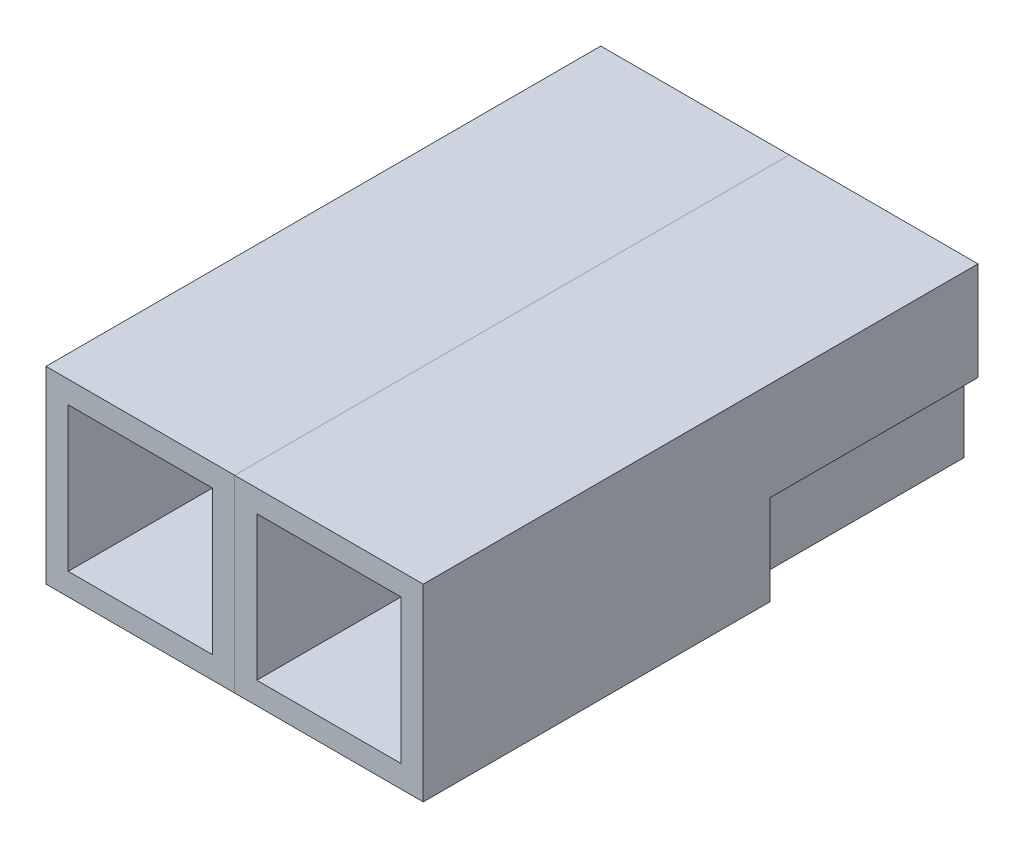
SolidWorks part; units mm, degrees
ref_plane "Front Plane" through (0, 0, 0) normal (0, 0, 1) x (1, 0, 0)
ref_plane "Top Plane" through (0, 0, 0) normal (0, 1, 0) x (1, 0, 0)
ref_plane "Right Plane" through (0, 0, 0) normal (1, 0, 0) x (0, 0, -1)
sketch "Sketch1" plane through (0, 0, 0) normal (0, 0, 1) x (1, 0, 0)
  line L1 (-11.0964, -1.4955) -> (-2.4604, -1.4955)
  line L2 (-11.0964, -1.4955) -> (-11.0964, -10.1315)
  line L3 (-11.0964, -10.1315) -> (-2.4604, -10.1315)
  line L4 (-2.4604, -1.4955) -> (-2.4604, -10.1315)
  dimension "D1" = 8.636
  dimension "D2" = 8.636
extrude "Extrude1" add sketch "Sketch1" along normal blind 25.4
sketch "Sketch2" plane through (0, 0, 25.4) normal (0, 0, 1) x (1, 0, 0)
  line L0 (-11.0964, -1.4955) -> (-11.0964, -10.1315) construction
  line L1 (-10.0804, -2.5115) -> (-3.4764, -2.5115)
  line L2 (-10.0804, -2.5115) -> (-10.0804, -9.1155)
  line L3 (-10.0804, -9.1155) -> (-3.4764, -9.1155)
  line L4 (-3.4764, -2.5115) -> (-3.4764, -9.1155)
  line L5 (-2.4604, -10.1315) -> (-2.4604, -1.4955) construction
  line L6 (-2.4604, -1.4955) -> (-11.0964, -1.4955) construction
  line L7 (-11.0964, -10.1315) -> (-2.4604, -10.1315) construction
  dimension "D1" = 1.016
  dimension "D2" = 1.016
  dimension "D3" = 1.016
  dimension "D4" = 1.016
extrude "Extrude2" cut sketch "Sketch2" against normal blind 12.7
sketch "Sketch3" plane through (0, 0, 0) normal (0, 0, -1) x (-1, 0, 0)
  line L4 (2.9684, -2.0035) -> (2.9684, -6.0053)
  line L5 (10.5884, -2.0035) -> (10.5884, -6.0053)
  line L7 (2.9684, -6.0053) -> (10.5884, -6.0053)
  line L8 (10.5884, -9.6235) -> (10.5884, -2.0035)
  line L9 (10.5884, -2.0035) -> (2.9684, -2.0035)
  line L10 (2.9684, -2.0035) -> (2.9684, -9.6235)
  line L11 (2.9684, -9.6235) -> (10.5884, -9.6235)
  line L13 (10.5884, -2.0035) -> (2.9684, -2.0035)
  dimension "D1" = 0.508
extrude "Extrude3" cut sketch "Sketch3" against normal blind 9.525
sketch "Sketch4" plane through (0, 0, 0) normal (0, 0, -1) x (-1, 0, 0)
  line L4 (2.9684, -6.0053) -> (10.5884, -6.0053) construction
  line L6 (3.0954, -6.0053) -> (3.0954, -9.4965)
  line L7 (3.0954, -9.4965) -> (10.4614, -9.4965)
  line L8 (11.0964, -10.1315) -> (11.0964, -1.4955)
  line L9 (11.0964, -1.4955) -> (2.4604, -1.4955)
  line L10 (2.4604, -1.4955) -> (2.4604, -10.1315)
  line L11 (2.4604, -10.1315) -> (11.0964, -10.1315)
  line L12 (3.0954, -6.0053) -> (2.4604, -6.0053)
  line L13 (10.4614, -6.0053) -> (10.4614, -9.4965)
  line L14 (2.4604, -10.1315) -> (2.4604, -1.4955) construction
  line L15 (2.4604, -10.1315) -> (11.0964, -10.1315)
  line L16 (2.4604, -6.0053) -> (2.4604, -10.1315)
  line L17 (10.4614, -6.0053) -> (11.0964, -6.0053)
  line L18 (11.0964, -1.4955) -> (11.0964, -10.1315) construction
  line L19 (11.0964, -6.0053) -> (11.0964, -10.1315)
  line L20 (11.0964, -10.1315) -> (11.0701, -10.1254)
  dimension "D2" = 0.635
  dimension "D1" = 0
extrude "Extrude4" cut sketch "Sketch4" against normal blind 9.525 contours L15 L16 L12 L6 L7 L13 L17 L19
pattern_linear "LPattern1" count 2 spacing 8.636 along (-1, 0, 0) of bodies 104
ref_plane "Plane1" through (-11.0964, 0, 0) normal (1, 0, 0) x (0, 0, -1)
